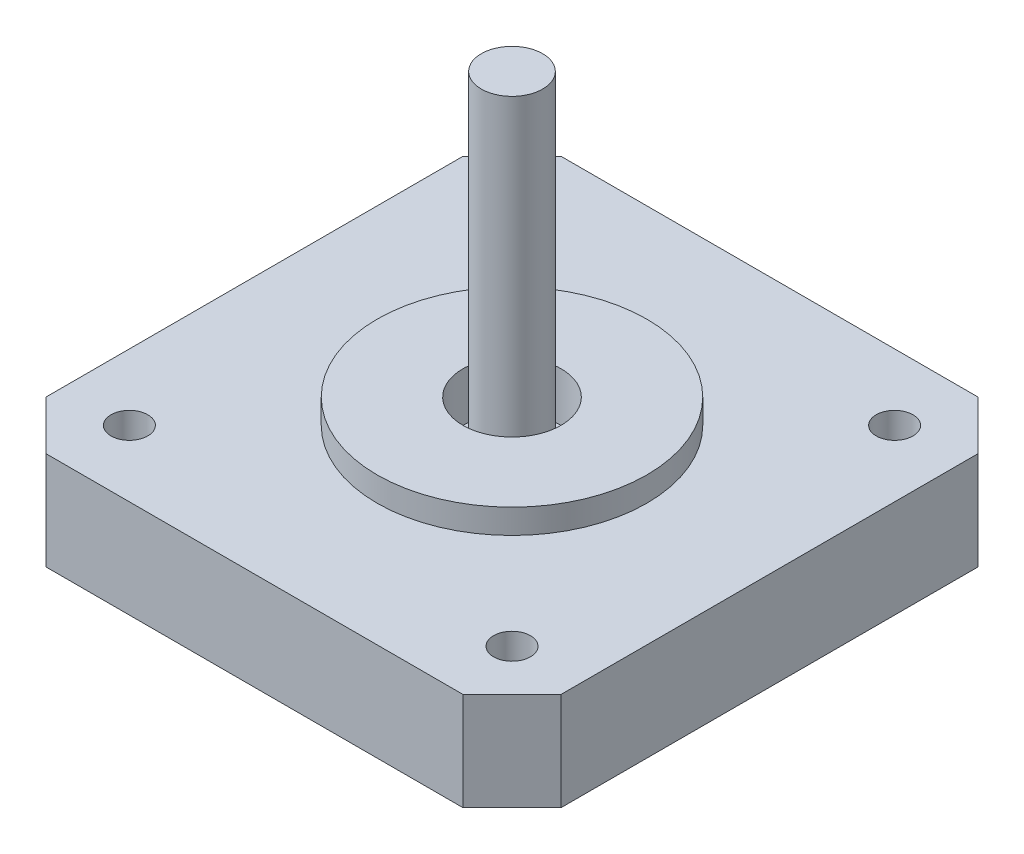
SolidWorks part; units mm, degrees
ref_plane "Front Plane" through (0, 0, 0) normal (0, 0, 1) x (1, 0, 0)
ref_plane "Top Plane" through (0, 0, 0) normal (0, 1, 0) x (1, 0, 0)
ref_plane "Right Plane" through (0, 0, 0) normal (1, 0, 0) x (0, 0, -1)
sketch "Sketch1" plane through (0, 0, 0) normal (0, 1, 0) x (1, 0, 0)
  line L1 (-21, 21) -> (21, 21)
  line L2 (-21, 21) -> (-21, -21)
  line L3 (-21, -21) -> (21, -21)
  line L4 (21, 21) -> (21, -21)
  point P4 (0, 21)
  point P6 (21, 0)
  dimension "D1" = 42
  dimension "D2" = 42
extrude "Boss-Extrude1" add sketch "Sketch1" along normal blind 8
sketch "Sketch2" plane through (0, 8, 0) normal (0, 1, 0) x (-1, 0, 0)
  circle A0 centre (0, 0) radius 11
  dimension "D1" = 22
extrude "Boss-Extrude2" add sketch "Sketch2" along normal blind 2
sketch "Sketch3" plane through (0, 10, 0) normal (0, 1, 0) x (1, 0, 0)
  circle A0 centre (0, 0) radius 4
extrude "Cut-Extrude1" cut sketch "Sketch3" against normal blind 4
sketch "Sketch4" plane through (0, 6, 0) normal (0, 1, 0) x (1, 0, 0)
  circle A0 centre (0, 0) radius 2.5
extrude "Boss-Extrude3" add sketch "Sketch4" along normal blind 27
chamfer "Chamfer1" distance 4 angle 45 4 edges at (-21, 4, -21) (21, 4, -21) (21, 4, 21) (-21, 4, 21)
sketch "Sketch5" plane through (0, 8, 0) normal (0, 1, 0) x (1, 0, 0)
  line L0 (-21, 17) -> (-21, -17) construction
  line L1 (17, 21) -> (-17, 21) construction
  line L2 (-17, -21) -> (17, -21) construction
  line L3 (21, -17) -> (21, 17) construction
  circle A0 centre (-15.6, 15.6) radius 1.5
  circle A1 centre (15.6, 15.6) radius 1.5
  circle A2 centre (15.6, -15.6) radius 1.5
  circle A3 centre (-15.6, -15.6) radius 1.5
  dimension "D1" = 5.4
  dimension "D2" = 5.4
  dimension "D3" = 5.4
  dimension "D4" = 5.4
  dimension "D5" = 5.4
  dimension "D6" = 5.4
  dimension "D7" = 5.4
  dimension "D8" = 5.4
extrude "Cut-Extrude2" cut sketch "Sketch5" against normal through all and the other way through all
